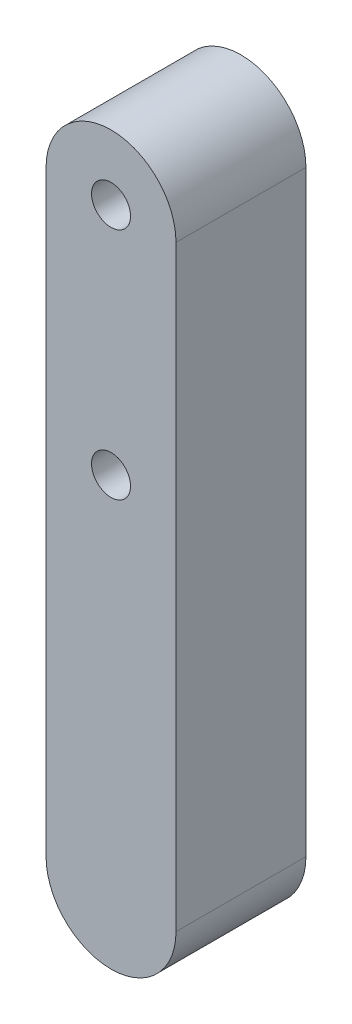
SolidWorks part; units mm, degrees
material "3D_printed_PLA"
ref_plane "Front Plane" through (0, 0, 0) normal (0, 0, 1) x (1, 0, 0)
ref_plane "Top Plane" through (0, 0, 0) normal (0, 1, 0) x (1, 0, 0)
ref_plane "Right Plane" through (0, 0, 0) normal (1, 0, 0) x (0, 0, -1)
sketch "Sketch2" plane through (0, 0, 0) normal (0, 0, -1) x (-1, 0, 0)
  line L0 (0, -18) -> (0, 18) construction
  line L5 (0, 18) -> (0, -73.8773) construction
  line L6 (10, 18) -> (10, -73.8773)
  line L7 (-10, 18) -> (-10, -73.8773)
  circle A2 centre (0, -18) radius 3
  circle A3 centre (0, 18) radius 3
  arc A6 (10, 18) -> (-10, 18) centre (0, 18) ccw
  arc A7 (-10, -73.8773) -> (10, -73.8773) centre (0, -73.8773) ccw
  point P0 (0, -27.9387)
  point P2 (0, 0)
  dimension "D1" = 6
  dimension "D2" = 20
  dimension "D4" = 36
extrude "Boss-Extrude3" add sketch "Sketch2" along normal blind 20
